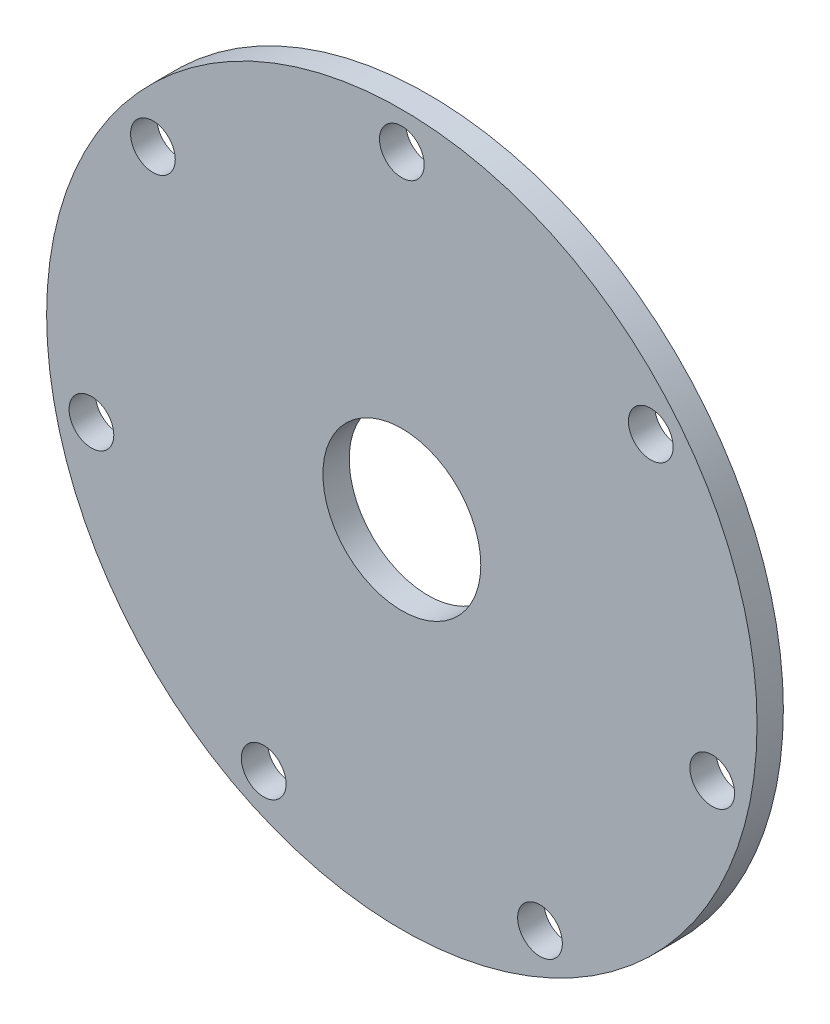
SolidWorks part; units mm, degrees
ref_plane "Plan de face" through (0, 0, 0) normal (0, 0, 1) x (1, 0, 0)
ref_plane "Plan de dessus" through (0, 0, 0) normal (0, 1, 0) x (1, 0, 0)
ref_plane "Plan de droite" through (0, 0, 0) normal (1, 0, 0) x (0, 0, -1)
sketch "Esquisse1" plane through (0, 0, 0) normal (0, 0, 1) x (1, 0, 0)
  circle A0 centre (0, 0) radius 67.5
  circle A1 centre (0, 60.5) radius 4.25
  circle A2 centre (47.3008, 37.7211) radius 4.25
  circle A3 centre (58.9831, -13.4625) radius 4.25
  circle A4 centre (26.25, -54.5086) radius 4.25
  circle A5 centre (-26.25, -54.5086) radius 4.25
  circle A6 centre (-58.9831, -13.4625) radius 4.25
  circle A7 centre (-47.3008, 37.7211) radius 4.25
  circle A8 centre (0, 0) radius 15
  point P19 (0, 0)
  dimension "D1" = 135
  dimension "D2" = 8.5
  dimension "D5" = 30
  dimension "D3" = 60.5
  dimension "D4" = 7
sketch "Esquisse2" [suppressed] plane through (0, 0, 0) normal (0, 0, 1) x (1, 0, 0)
  line L0 (0, 0) -> (-60.9953, 28.9105) construction
  line L1 (0, 0) -> (60.9953, 28.9105) construction
  line L2 (0, 0) -> (0, 67.5) construction
  line L3 (-32.9407, 41.8387) -> (-41.7558, 53.0349)
  line L4 (-12.1726, 51.84) -> (-15.4301, 65.7127)
  line L5 (12.1726, 51.84) -> (15.4301, 65.7127)
  line L6 (32.9407, 41.8387) -> (41.7558, 53.0349)
  line L7 (-48.1185, 22.8072) -> (-60.9953, 28.9105)
  line L8 (48.1185, 22.8072) -> (60.9953, 28.9105)
  line L9 (0, 0) -> (-47.3008, 37.7211) construction
  line L10 (0, 0) -> (-32.9407, 41.8387)
  line L11 (-49.4267, 23.4272) -> (-33.8366, 42.9766)
  line L12 (-12.5037, 53.25) -> (12.5037, 53.25)
  line L13 (33.8366, 42.9766) -> (49.4267, 23.4272)
  line L14 (0, 0) -> (47.3008, 37.7211) construction
  circle A0 centre (47.3008, 37.7211) radius 4.25 construction
  circle A1 centre (0, 60.5) radius 4.25 construction
  circle A2 centre (-47.3008, 37.7211) radius 4.25 construction
  circle A3 centre (47.3008, 37.7211) radius 4.25
  circle A4 centre (0, 60.5) radius 4.25
  circle A5 centre (-47.3008, 37.7211) radius 4.25
  circle A6 centre (0, 0) radius 67.5 construction
  arc A7 (-60.9953, 28.9105) -> (60.9953, 28.9105) centre (0, 0) cw
  arc A8 (-48.1185, 22.8072) -> (48.1185, 22.8072) centre (0, 0) cw
  arc A9 (-40.0546, 50.8742) -> (-14.8014, 63.0355) centre (0, 0) cw
  arc A10 (14.8014, 63.0355) -> (40.0546, 50.8742) centre (0, 0) cw
  arc A11 (-47.3008, 37.7211) -> (-37.4256, 47.535) centre (0, 0) cw construction
  arc A12 (0, 60.5) -> (-13.8299, 58.8981) centre (0, 0) ccw construction
  dimension "D3" = 53.25
  dimension "D6" = 64.75
  dimension "D1" = 64.64
  dimension "D2" = 64.64
  dimension "D4" = 25
  dimension "D5" = 25
  dimension "D7" = 13.211
  dimension "D8" = 13.214
extrude "Boss.-Extru.1" add sketch "Esquisse1" along normal blind 5
